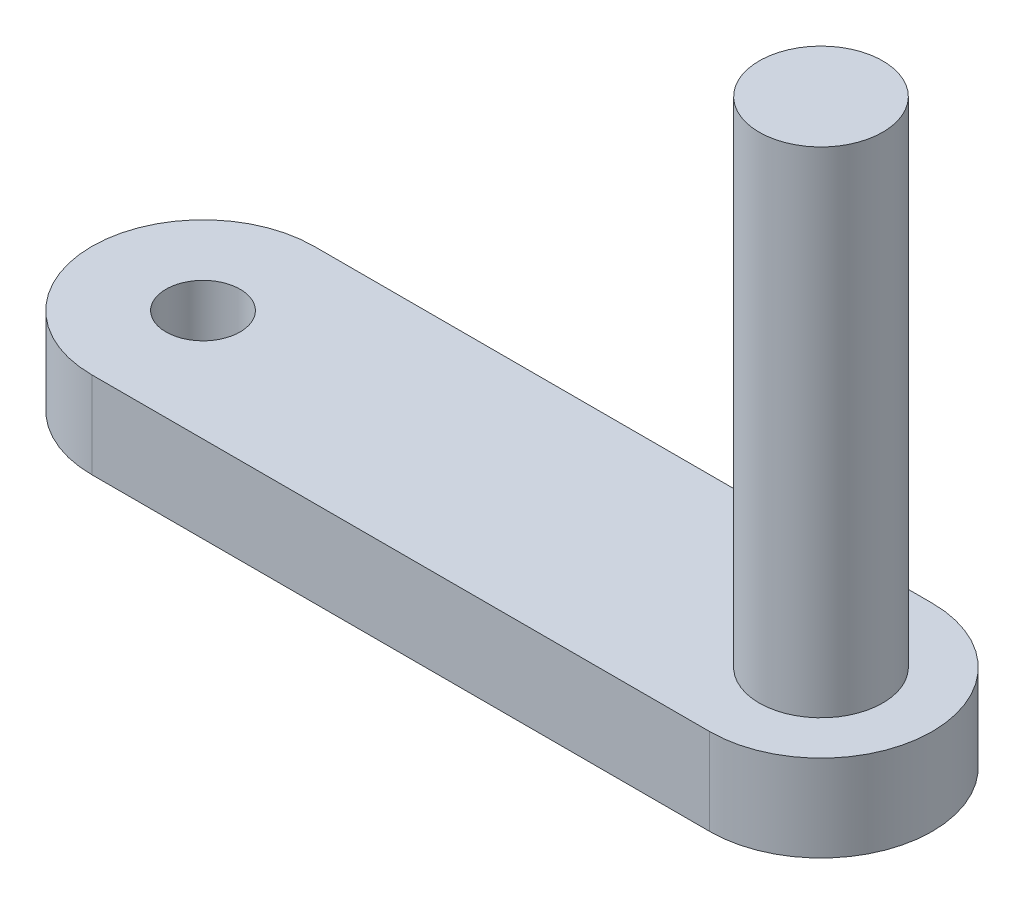
SolidWorks part; units mm, degrees
ref_plane "Front Plane" through (0, 0, 0) normal (0, 0, 1) x (1, 0, 0)
ref_plane "Top Plane" through (0, 0, 0) normal (0, 1, 0) x (1, 0, 0)
ref_plane "Right Plane" through (0, 0, 0) normal (1, 0, 0) x (0, 0, -1)
sketch "Sketch1" plane through (0, 0, 0) normal (0, 1, 0) x (1, 0, 0)
  line L0 (-25, 0) -> (25, 0) construction
  line L1 (-25, 9) -> (25, 9)
  line L2 (-25, -9) -> (25, -9)
  arc A0 (-25, 9) -> (-25, -9) centre (-25, 0) ccw
  arc A1 (25, -9) -> (25, 9) centre (25, 0) ccw
  circle A2 centre (25, 0) radius 4
  circle A3 centre (-25, 0) radius 3
  point P2 (0, 0)
  dimension "D2" = 9
  dimension "D3" = 6
  dimension "D4" = 8
  dimension "D1" = 50
extrude "Boss-Extrude1" add sketch "Sketch1" along normal blind 7
sketch "Sketch2" plane through (0, 7, 0) normal (0, 1, 0) x (1, 0, 0)
  circle A0 centre (25, 0) radius 5
  dimension "D1" = 10
extrude "Boss-Extrude2" add sketch "Sketch2" along normal blind 40
